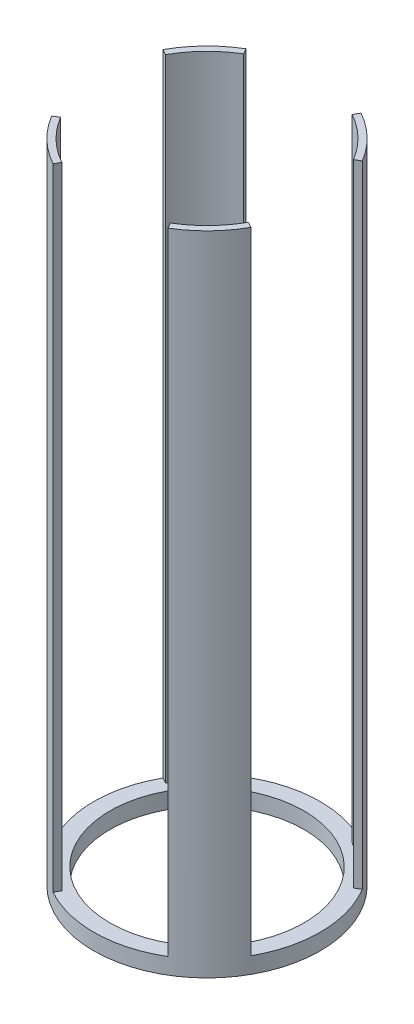
SolidWorks part; units mm, degrees
ref_plane "Front Plane" through (0, 0, 0) normal (0, 0, 1) x (1, 0, 0)
ref_plane "Top Plane" through (0, 0, 0) normal (0, 1, 0) x (1, 0, 0)
ref_plane "Right Plane" through (0, 0, 0) normal (1, 0, 0) x (0, 0, -1)
sketch "Sketch2" plane through (0, 0, 0) normal (0, 1, 0) x (1, 0, 0)
  circle A0 centre (0, 0) radius 88.9
  circle A1 centre (0, 0) radius 83.82
  dimension "D1" = 177.8
  dimension "D2" = 167.64
extrude "Boss-Extrude1" add sketch "Sketch2" along normal mid plane 508
sketch "Sketch3" plane through (0, 0, 0) normal (0, 1, 0) x (1, 0, 0)
  line L0 (0, 0) -> (169.6618, 101.6776)
  line L1 (-58.1167, 96.9749) -> (0, 0)
  line L2 (0, 0) -> (53.9, 96.9749)
  line L3 (53.9, 96.9749) -> (-58.1167, 96.9749)
  line L4 (0, 0) -> (70.9917, -118.4586)
  line L5 (70.9917, -118.4586) -> (-65.8409, -118.4586)
  line L6 (-65.8409, -118.4586) -> (0, 0)
  line L7 (169.6618, 101.6776) -> (169.6618, -94.3004)
  line L8 (169.6618, -94.3004) -> (0, 0)
  line L9 (0, 0) -> (-123.7413, 68.7771)
  line L10 (-123.7413, 68.7771) -> (-123.7413, -74.1577)
  line L11 (-123.7413, -74.1577) -> (0, 0)
  dimension "D1" = 60
  dimension "D2" = 60
  dimension "D3" = 60
  dimension "D4" = 60
  dimension "D5" = 30
  dimension "D6" = 30
extrude "Cut-Extrude1" cut sketch "Sketch3" against normal through all both and the other way through all contours L8 L7 L0 | L2 L3 L1 | L10 L11 L9 | L6 L5 L4
sketch "Sketch4" plane through (0, -254, 0) normal (0, -1, 0) x (1, 0, 0)
  circle A0 centre (0, 0) radius 88.9
  circle A1 centre (0, 0) radius 76.2
  dimension "D1" = 152.4
  dimension "D2" = 177.8
extrude "Boss-Extrude2" add sketch "Sketch4" against normal blind 12.7
equation "\"D1@Boss-Extrude1\"=3*12"
